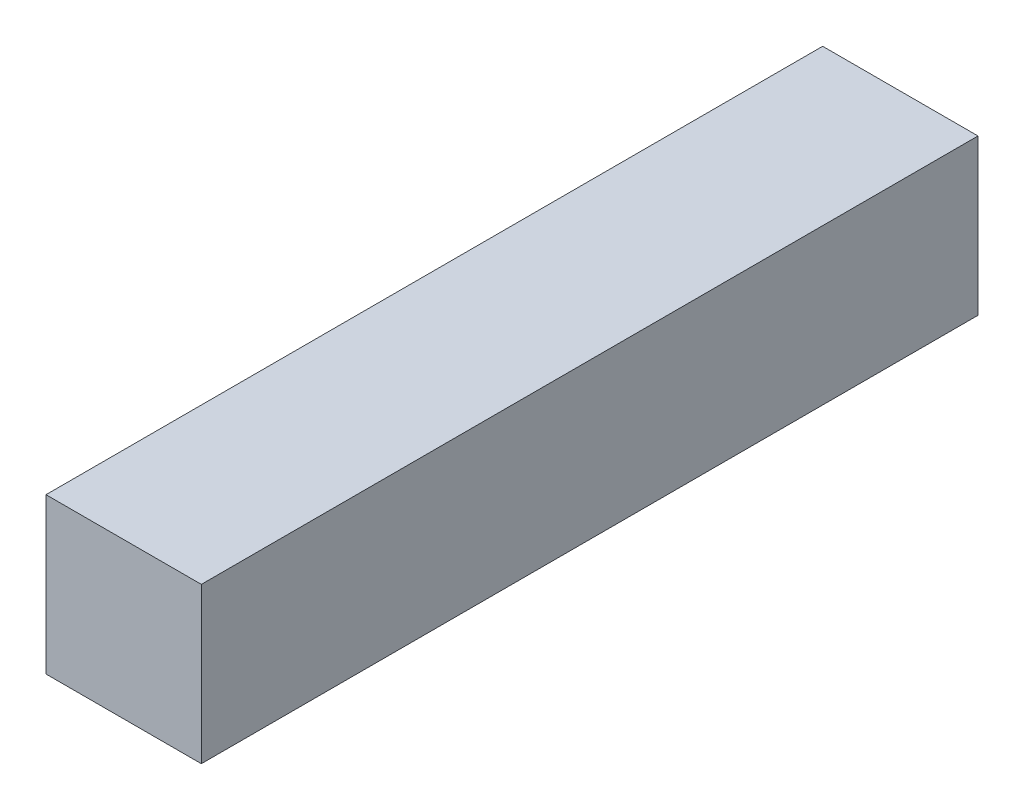
SolidWorks part; units mm, degrees
ref_plane "Front Plane" through (0, 0, 0) normal (0, 0, 1) x (1, 0, 0)
ref_plane "Top Plane" through (0, 0, 0) normal (0, 1, 0) x (1, 0, 0)
ref_plane "Right Plane" through (0, 0, 0) normal (1, 0, 0) x (0, 0, -1)
sketch "Sketch1" plane through (0, 0, 0) normal (0, 0, 1) x (1, 0, 0)
  line L1 (3.175, 3.175) -> (-3.175, 3.175)
  line L2 (3.175, 3.175) -> (3.175, -3.175)
  line L3 (3.175, -3.175) -> (-3.175, -3.175)
  line L4 (-3.175, 3.175) -> (-3.175, -3.175)
  line L5 (3.175, 3.175) -> (-3.175, -3.175) construction
  line L6 (3.175, -3.175) -> (-3.175, 3.175) construction
  point P0 (0, 0)
  dimension "D1" = 6.35
extrude "Boss-Extrude1" add sketch "Sketch1" along normal blind 31.75
